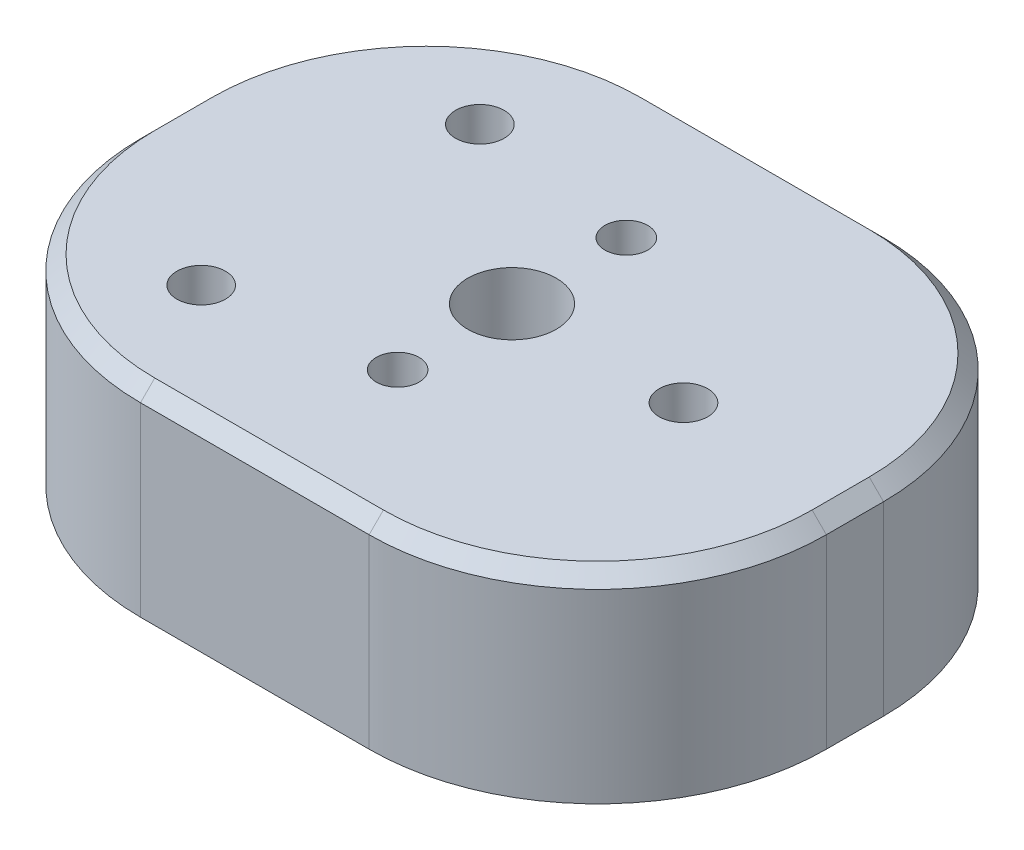
SolidWorks part; units mm, degrees
ref_plane "Front Plane" through (0, 0, 0) normal (0, 0, 1) x (1, 0, 0)
ref_plane "Top Plane" through (0, 0, 0) normal (0, 1, 0) x (1, 0, 0)
ref_plane "Right Plane" through (0, 0, 0) normal (1, 0, 0) x (0, 0, -1)
sketch "Sketch1" plane through (0, 0, 0) normal (0, 1, 0) x (1, 0, 0)
  line L0 (-12, 9.75) -> (-12, -9.75) construction
  line L1 (-12, -9.75) -> (12, 0) construction
  line L2 (12, 0) -> (-12, 9.75) construction
  line L3 (-12, 0) -> (12, 0) construction
  line L5 (-24, -18) -> (24, -18)
  line L6 (-24, -18) -> (-24, 18)
  line L7 (-24, 18) -> (24, 18)
  line L8 (24, -18) -> (24, 18)
  line L9 (-24, -18) -> (24, 18) construction
  line L10 (-24, 18) -> (24, -18) construction
  circle A0 centre (-12, 9.75) radius 1.7
  circle A1 centre (-12, -9.75) radius 1.7
  circle A2 centre (12, 0) radius 1.7
  point P7 (0, 0)
  point P8 (0, 0)
  dimension "D1" = 3.4
  dimension "D2" = 19.5
  dimension "D3" = 24
  dimension "D4" = 48
  dimension "D5" = 36
extrude "Boss-Extrude1" add sketch "Sketch1" along normal blind 14
sketch "Sketch2" plane through (0, 0, 0) normal (0, -1, 0) x (1, 0, 0)
  line L0 (0, 8) -> (0, -8) construction
  circle A0 centre (0, 0) radius 14.5 construction
  circle A1 centre (0, 8) radius 1.5
  circle A2 centre (0, -8) radius 1.5
  circle A3 centre (0, 0) radius 3.1
  point P8 (0, 0)
  dimension "D1" = 29
  dimension "D3" = 3
  dimension "D4" = 6.2
  dimension "D2" = 16
extrude "Cut-Extrude3" cut sketch "Sketch2" against normal through all
sketch "Sketch5" plane through (0, 0, 0) normal (0, -1, 0) x (1, 0, 0)
  circle A0 centre (0, 0) radius 15
  circle A1 centre (0, 0) radius 18
  dimension "D1" = 30
extrude "Cut-Extrude4" cut sketch "Sketch5" against normal blind 3 contours A0
sketch "Sketch7" plane through (0, 0, 0) normal (0, -1, 0) x (1, 0, 0)
  circle A0 centre (12, 0) radius 4.75
  circle A1 centre (-12, 9.75) radius 4.75
  circle A2 centre (-12, -9.75) radius 4.75
  dimension "D1" = 9.5
  dimension "D2" = 9.5
  dimension "D3" = 9.5
extrude "Cut-Extrude5" cut sketch "Sketch7" against normal blind 6
fillet "Fillet1" radius 16 2 edges at (24, 7, 18) (24, 7, -18)
fillet "Fillet2" radius 16 2 edges at (-24, 7, 18) (-24, 7, -18)
fillet "Fillet3" radius 0.5 6 edges at (-15.6865, 0, -12.7453) (-15, 0, 0) (-15.6865, 0, 12.7453) (5.2746, 0, 14.042) (16.75, 0, 0) (5.2746, 0, -14.042)
chamfer "Chamfer2" distance 1 angle 45 8 edges at (19.3137, 14, -13.3137) (0, 14, -18) (24, 14, 0) (-19.3137, 14, -13.3137) (19.3137, 14, 13.3137) (-24, 14, 0) (0, 14, 18) (-19.3137, 14, 13.3137)
